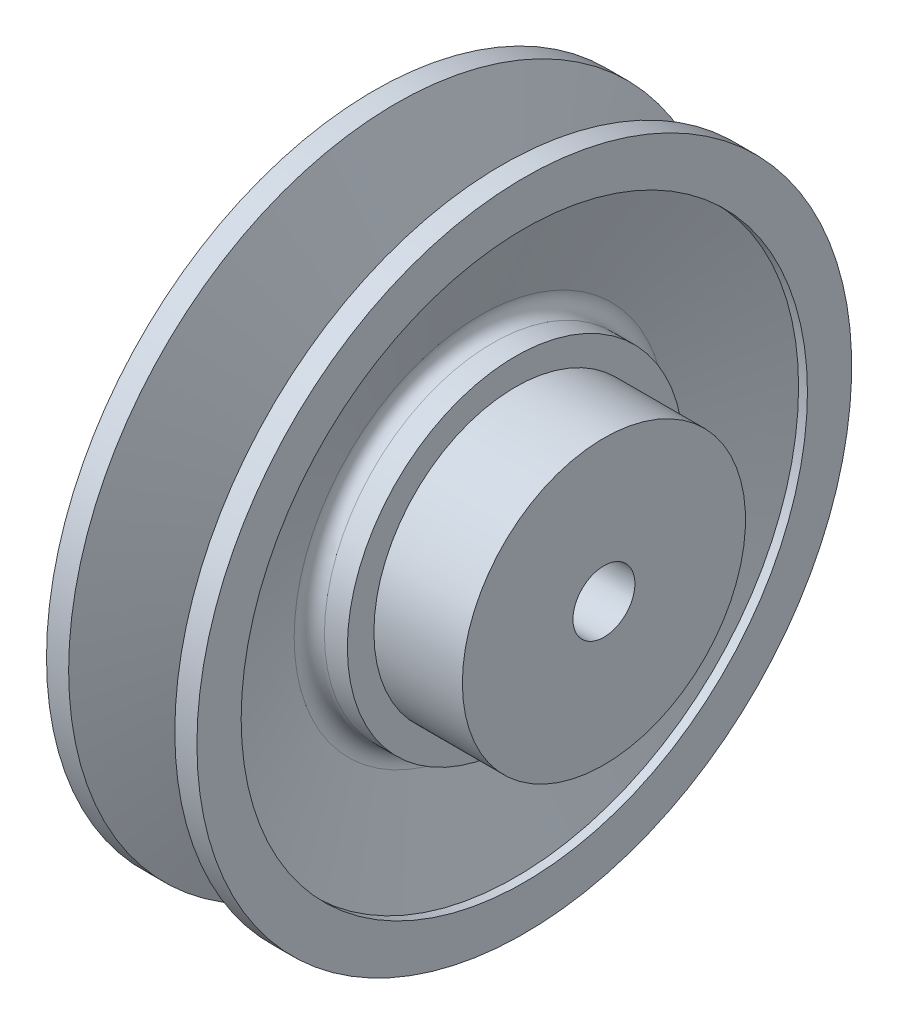
SolidWorks part; units mm, degrees
ref_plane "Frontal" through (0, 0, 0) normal (0, 0, 1) x (1, 0, 0)
ref_plane "Horizontal" through (0, 0, 0) normal (0, 1, 0) x (1, 0, 0)
ref_plane "Profile" through (0, 0, 0) normal (1, 0, 0) x (0, 0, -1)
sketch "Sketch1" plane through (0, 0, 0) normal (0, 0, 1) x (1, 0, 0)
  line L0 (-36.252, 8.1485) -> (13.748, 8.1485)
  line L1 (13.748, 8.1485) -> (13.748, 33.1485)
  line L2 (13.748, 33.1485) -> (-6.252, 33.1485)
  line L3 (-6.252, 33.1485) -> (-6.252, 39.1485)
  line L4 (-6.252, 39.1485) -> (-15.7152, 39.1485)
  line L5 (-36.252, 65.1485) -> (-26.7888, 39.1485)
  line L6 (-6.252, 65.1485) -> (-15.7152, 39.1485)
  line L7 (-4.252, 75.1485) -> (-4.252, 65.1485)
  line L8 (-4.252, 75.1485) -> (-9.252, 75.1485)
  line L9 (-9.252, 75.1485) -> (-18.3512, 50.1485)
  line L10 (-18.3512, 50.1485) -> (-24.1527, 50.1485)
  line L11 (-24.1527, 50.1485) -> (-33.252, 75.1485)
  line L12 (-33.252, 75.1485) -> (-38.252, 75.1485)
  line L13 (-38.252, 75.1485) -> (-38.252, 65.1485)
  line L14 (-66.2035, 1.1485) -> (51.9243, 1.1485) construction
  line L15 (-36.252, 39.1485) -> (-36.252, 8.1485)
  line L16 (-38.252, 65.1485) -> (-36.252, 65.1485)
  line L17 (-26.7888, 39.1485) -> (-36.252, 39.1485)
  line L19 (-4.252, 65.1485) -> (-6.252, 65.1485)
  dimension "D1" = 50
  dimension "D2" = 30
  dimension "D3" = 34
  dimension "D4" = 5
  dimension "D5" = 2
  dimension "D6" = 25
  dimension "D7" = 36
  dimension "D8" = 25
  dimension "D9" = 40
  dimension "D10" = 10
  dimension "D11" = 67
  dimension "D12" = 7
revolve "Revolve1" add sketch "Sketch1" angle 360 about L14
fillet "Fillet2" radius 3 4 edges at (-26.7888, 1.1485, 38) (-24.1527, 1.1485, 49) (-18.3512, 1.1485, 49) (-15.7152, 1.1485, 38)
